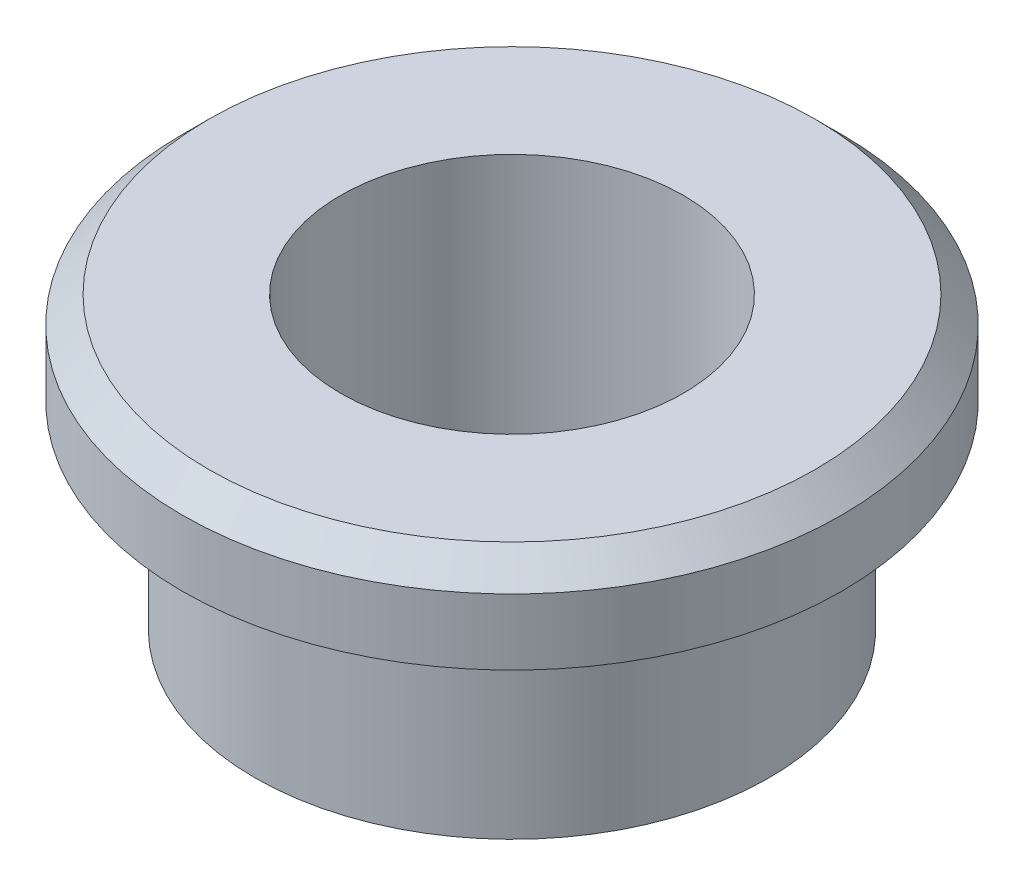
SolidWorks part; units mm, degrees
material "High-leaded brass, UNS C34200"
ref_plane "Front Plane" through (0, 0, 0) normal (0, 0, 1) x (1, 0, 0)
ref_plane "Top Plane" through (0, 0, 0) normal (0, 1, 0) x (1, 0, 0)
ref_plane "Right Plane" through (0, 0, 0) normal (1, 0, 0) x (0, 0, -1)
sketch "Sketch1" plane through (0, 0, 0) normal (0, 0, 1) x (1, 0, 0)
  line L0 (0, 9.7911) -> (0, 0) construction
  line L1 (2.6, 4.4) -> (2.6, 0)
  line L2 (2.6, 0) -> (3.9, 0)
  line L3 (3.9, 0) -> (3.9, 3)
  line L4 (3.9, 3) -> (5, 3)
  line L5 (5, 3) -> (5, 4)
  line L6 (5, 4) -> (4.6, 4.4)
  line L7 (4.6, 4.4) -> (2.6, 4.4)
  dimension "D1" = 2.6
  dimension "D2" = 5
  dimension "D3" = 3
  dimension "D4" = 1.4
  dimension "D5" = 135
  dimension "D6" = 0.4
  dimension "D7" = 3.9
revolve "Revolve1" add sketch "Sketch1" angle 360 about L0
